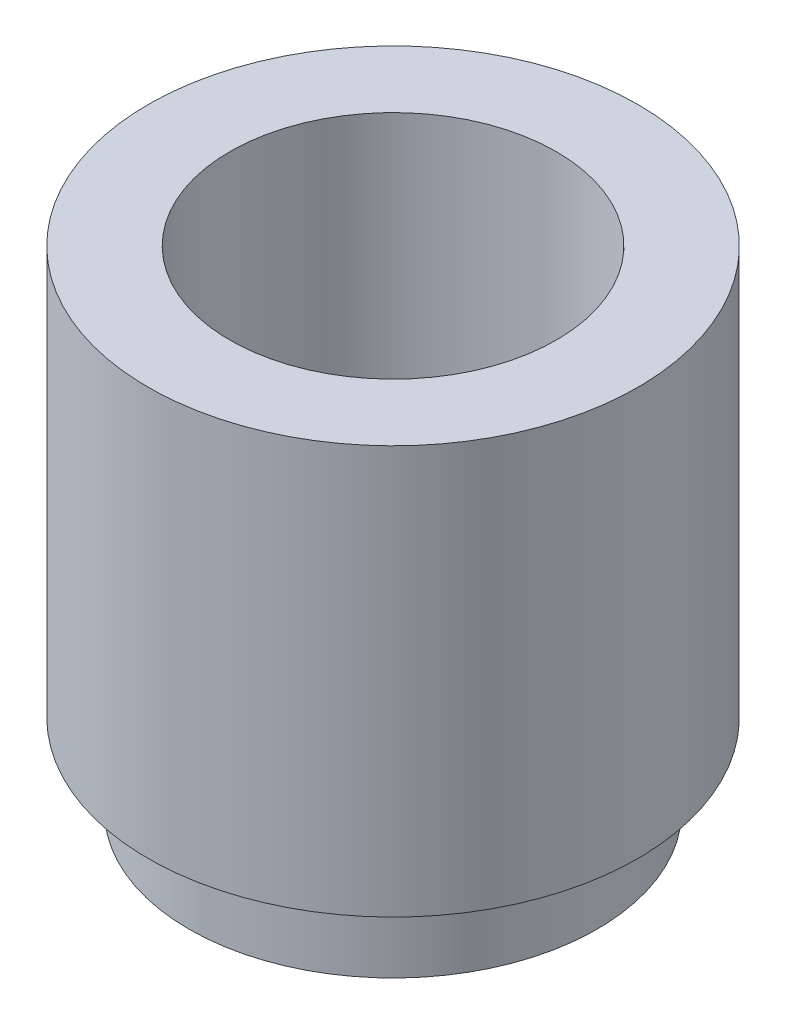
SolidWorks part; units mm, degrees
material "Brass"
ref_plane "Front Plane" through (0, 0, 0) normal (0, 0, 1) x (1, 0, 0)
ref_plane "Top Plane" through (0, 0, 0) normal (0, 1, 0) x (1, 0, 0)
ref_plane "Right Plane" through (0, 0, 0) normal (1, 0, 0) x (0, 0, -1)
sketch "Sketch1" plane through (0, 0, 0) normal (1, 0, 0) x (0, 0, -1)
  line L0 (0, 0) -> (0, 6) construction
  line L1 (2, 6) -> (2, 0)
  line L2 (2, 0) -> (2.5, 0)
  line L3 (2.5, 0) -> (2.5, 1)
  line L4 (2.5, 1) -> (3, 1)
  line L5 (3, 1) -> (3, 6)
  line L6 (3, 6) -> (2, 6)
  point P5 (0, 0)
  dimension "D1" = 6
  dimension "D2" = 6
  dimension "D3" = 4
  dimension "D4" = 5
  dimension "D5" = 1
revolve "Revolve1" add sketch "Sketch1" angle 360 about L0
